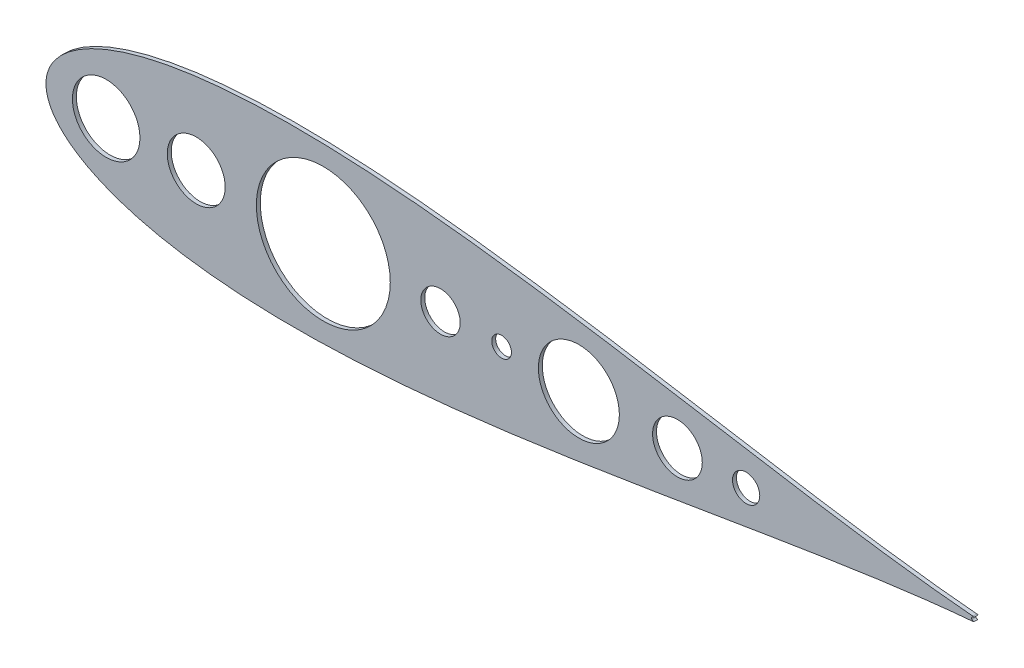
SolidWorks part; units mm, degrees
ref_plane "Front Plane" through (0, 0, 0) normal (0, 0, 1) x (1, 0, 0)
ref_plane "Top Plane" through (0, 0, 0) normal (0, 1, 0) x (1, 0, 0)
ref_plane "Right Plane" through (0, 0, 0) normal (1, 0, 0) x (0, 0, -1)
sketch "Model" plane through (0, 0, 0) normal (0, 0, 1) x (1, 0, 0)
  line L0 (786.347, 515.344) -> (786.347, 515.865)
  line L1 (784.9141, 514.1717) -> (785.37, 514.1717)
  line L2 (785.5654, 516.7117) -> (785.1095, 516.7117)
  line L3 (784.0675, 516.0604) -> (783.1903, 516.0604)
  line L4 (784.0675, 516.386) -> (784.0675, 516.0604)
  line L5 (783.2391, 516.386) -> (784.0675, 516.386)
  line L6 (783.4834, 518.0142) -> (783.2391, 516.386)
  line L7 (783.0906, 518.0142) -> (783.4834, 518.0142)
  line L8 (782.8463, 516.386) -> (783.0906, 518.0142)
  line L9 (782.0505, 518.0142) -> (781.8063, 516.386)
  line L10 (781.6577, 518.0142) -> (782.0505, 518.0142)
  line L11 (781.4135, 516.386) -> (781.6577, 518.0142)
  line L12 (780.4203, 516.386) -> (781.4135, 516.386)
  line L13 (780.4203, 516.0604) -> (780.4203, 516.386)
  line L14 (781.3647, 516.0604) -> (780.4203, 516.0604)
  line L15 (781.1886, 514.8881) -> (781.3647, 516.0604)
  line L16 (780.29, 514.8881) -> (781.1886, 514.8881)
  line L17 (780.29, 514.5625) -> (780.29, 514.8881)
  line L18 (781.1398, 514.5625) -> (780.29, 514.5625)
  line L19 (780.8762, 512.804) -> (781.1398, 514.5625)
  line L20 (781.27, 512.804) -> (780.8762, 512.804)
  line L21 (781.5336, 514.5625) -> (781.27, 512.804)
  line L22 (782.5726, 514.5625) -> (781.5336, 514.5625)
  line L23 (782.309, 512.804) -> (782.5726, 514.5625)
  line L24 (782.7028, 512.804) -> (782.309, 512.804)
  line L25 (782.9664, 514.5625) -> (782.7028, 512.804)
  line L26 (783.9372, 514.5625) -> (782.9664, 514.5625)
  line L27 (783.9372, 514.8881) -> (783.9372, 514.5625)
  line L28 (783.0153, 514.8881) -> (783.9372, 514.8881)
  line L29 (783.1903, 516.0604) -> (783.0153, 514.8881)
  line L30 (781.8063, 516.386) -> (782.8463, 516.386)
  line L31 (781.5824, 514.8881) -> (782.6214, 514.8881)
  line L32 (782.7975, 516.0604) -> (781.7575, 516.0604)
  line L33 (782.6214, 514.8881) -> (782.7975, 516.0604)
  line L34 (781.7575, 516.0604) -> (781.5824, 514.8881)
  circle A0 centre (390.1313, 511.9487) radius 18.669
  circle A1 centre (547.6113, 511.9487) radius 12.7
  circle A2 centre (586.9813, 511.9487) radius 6.35
  circle A3 centre (700.3234, 511.9487) radius 16.0288
  circle A4 centre (744.6175, 511.9487) radius 8.7799
  circle A5 centre (332.0731, 511.9487) radius 21.7634
  arc A6 (890.8162, 510.4774) -> (891.5484, 510.7448) centre (890.6938, 511.9487) ccw
  arc A7 (891.5489, 513.1522) -> (890.8162, 513.42) centre (890.6938, 511.9487) ccw
  arc A8 (891.5489, 513.1522) -> (891.5484, 510.7448) centre (891.2322, 511.9485) ccw
  circle A9 centre (636.7879, 511.9487) radius 26.1032
  circle A10 centre (472.0506, 511.9487) radius 43.167
  spline S0 degree 3 poles (890.8162, 513.42) (890.3349, 513.46) (886.7082, 513.7655) (879.5659, 514.4256) (868.9642, 515.5285) (857.2098, 516.8818) (844.3469, 518.4937) (830.4355, 520.3658) (815.5358, 522.4939) (799.7123, 524.867) (783.0322, 527.4682) (765.5654, 530.2744) (747.384, 533.2565) (728.5623, 536.3802) (709.1765, 539.6059) (689.3045, 542.8901) (669.0255, 546.185) (648.4208, 549.44) (627.5727, 552.6022) (606.5651, 555.6172) (585.4835, 558.4299) (564.4149, 560.9854) (543.4476, 563.23) (522.6717, 565.1117) (502.1785, 566.5817) (482.061, 567.5944) (462.4138, 568.109) (443.3327, 568.0899) (424.9152, 567.5068) (407.2601, 566.3367) (390.4682, 564.5628) (374.6421, 562.177) (359.8874, 559.1785) (346.3131, 555.5773) (334.0341, 551.3946) (323.1728, 546.6676) (313.8611, 541.4589) (306.2382, 535.8742) (300.4324, 530.0959) (296.5018, 524.4296) (294.31, 519.3174) (293.4249, 515.2165) (293.2233, 511.9487) (293.4249, 508.6808) (294.31, 504.5799) (296.5018, 499.4677) (300.4324, 493.8014) (306.2382, 488.0231) (313.8611, 482.4384) (323.1728, 477.2297) (334.0341, 472.5027) (346.3131, 468.32) (359.8874, 464.7188) (374.6421, 461.7204) (390.4682, 459.3346) (407.2601, 457.5606) (424.9152, 456.3906) (443.3327, 455.8074) (462.4138, 455.7883) (482.061, 456.3029) (502.1785, 457.3157) (522.6717, 458.7856) (543.4476, 460.6673) (564.4149, 462.9119) (585.4835, 465.4674) (606.5651, 468.2801) (627.5727, 471.2951) (648.4208, 474.4573) (669.0255, 477.7124) (689.3045, 481.0073) (709.1765, 484.2914) (728.5623, 487.5172) (747.384, 490.6408) (765.5654, 493.6229) (783.0322, 496.4291) (799.7123, 499.0303) (815.5358, 501.4035) (830.4355, 503.5316) (844.3469, 505.4037) (857.2098, 507.0155) (868.9642, 508.3689) (879.5659, 509.4717) (886.7082, 510.1319) (890.3349, 510.4373) (890.8162, 510.4774) knots 0.020157 0.020157 0.020157 0.020157 0.021271 0.028553 0.036781 0.04592 0.055932 0.066773 0.078397 0.090755 0.103793 0.117456 0.131686 0.146422 0.1616 0.177156 0.193024 0.209135 0.225421 0.241812 0.258238 0.274629 0.290914 0.307025 0.322893 0.338448 0.353626 0.368361 0.38259 0.396253 0.40929 0.421647 0.43327 0.444109 0.454119 0.463255 0.471479 0.478755 0.485052 0.490344 0.49461 0.497833 0.5 0.502167 0.50539 0.509656 0.514948 0.521245 0.528521 0.536745 0.545881 0.555891 0.56673 0.578353 0.59071 0.603747 0.61741 0.631639 0.646374 0.661552 0.677107 0.692975 0.709086 0.725371 0.741762 0.758188 0.774579 0.790865 0.806976 0.822844 0.8384 0.853578 0.868314 0.882544 0.896207 0.909245 0.921603 0.933227 0.944068 0.95408 0.963219 0.971447 0.978729 0.979843 0.979843 0.979843 0.979843
  spline S1 degree 3 poles (786.6085, 512.6737) (786.5542, 512.675) (786.4473, 512.6775) (786.2902, 512.6944) (786.1402, 512.7254) (785.9972, 512.767) (785.861, 512.8199) (785.732, 512.8856) (785.6095, 512.963) (785.4945, 513.0529) (785.3872, 513.1535) (785.2903, 513.2665) (785.2023, 513.3898) (785.1254, 513.525) (785.0563, 513.6702) (784.9994, 513.8273) (784.9494, 513.9949) (784.9261, 514.1118) (784.9141, 514.1717) knots 0 0 0 0 0.065541 0.128963 0.190377 0.250092 0.308548 0.366398 0.424542 0.48317 0.542243 0.601739 0.662506 0.724856 0.789128 0.856346 0.926295 1 1 1 1
  spline S2 degree 3 poles (786.6166, 513.1948) (786.6642, 513.1957) (786.7571, 513.1974) (786.8928, 513.2135) (787.0218, 513.2369) (787.1428, 513.273) (787.2574, 513.3177) (787.3639, 513.3738) (787.4638, 513.4396) (787.5557, 513.5144) (787.6383, 513.5963) (787.7111, 513.682) (787.773, 513.771) (787.8229, 513.864) (787.8623, 513.9604) (787.8891, 514.0607) (787.9078, 514.1639) (787.9093, 514.234) (787.91, 514.2694) knots 0 0 0 0 0.076072 0.148752 0.218403 0.28576 0.350598 0.414964 0.478069 0.541761 0.60435 0.664075 0.721464 0.777587 0.832644 0.887844 0.94346 1 1 1 1
  spline S3 degree 3 poles (785.7679, 513.4695) (785.7964, 513.4476) (785.8532, 513.4038) (785.9457, 513.3479) (786.0431, 513.2995) (786.1473, 513.2625) (786.2562, 513.2312) (786.3715, 513.2107) (786.4921, 513.1966) (786.5745, 513.1954) (786.6166, 513.1948) knots 0 0 0 0 0.118271 0.236178 0.355663 0.475904 0.600127 0.728608 0.861313 1 1 1 1
  spline S4 degree 3 poles (786.347, 515.865) (786.4098, 515.8661) (786.5329, 515.8682) (786.7127, 515.8934) (786.8847, 515.9284) (787.045, 515.9819) (787.1911, 516.0441) (787.3178, 516.1165) (787.4234, 516.1969) (787.5074, 516.2866) (787.5706, 516.3829) (787.6168, 516.4832) (787.6441, 516.5885) (787.6477, 516.6603) (787.6495, 516.6964) knots 0 0 0 0 0.110166 0.215787 0.318027 0.417574 0.51165 0.596162 0.672935 0.74367 0.810677 0.874059 0.936696 1 1 1 1
  spline S5 degree 3 poles (787.5122, 515.6493) (787.5662, 515.6232) (787.6733, 515.5715) (787.8192, 515.4701) (787.9517, 515.353) (788.0256, 515.2617) (788.0627, 515.2158) knots 0 0 0 0 0.25388 0.503009 0.750291 1 1 1 1
  spline S6 degree 3 poles (788.3659, 514.3131) (788.3633, 514.242) (788.3581, 514.1001) (788.3117, 513.8904) (788.2397, 513.6854) (788.1374, 513.4893) (788.0128, 513.3059) (787.8645, 513.1418) (787.6943, 513.0007) (787.5044, 512.8828) (787.2987, 512.7886) (787.0787, 512.7232) (786.8476, 512.6806) (786.6891, 512.6761) (786.6085, 512.6737) knots 0 0 0 0 0.079648 0.158922 0.239619 0.322609 0.406035 0.487602 0.569685 0.653036 0.737436 0.822478 0.909748 1 1 1 1
  spline S7 degree 3 poles (787.91, 514.2694) (787.9078, 514.3167) (787.9034, 514.4111) (787.8696, 514.5501) (787.8139, 514.6839) (787.736, 514.8104) (787.6412, 514.9277) (787.5303, 515.0323) (787.4026, 515.1186) (787.285, 515.1782) (787.1808, 515.2189) (787.0917, 515.246) (786.9919, 515.269) (786.8826, 515.2903) (786.7631, 515.3085) (786.6335, 515.3237) (786.4936, 515.3358) (786.3968, 515.3412) (786.347, 515.344) knots 0 0 0 0 0.066909 0.133485 0.201035 0.271234 0.34288 0.413836 0.485977 0.56023 0.599884 0.644055 0.691892 0.744688 0.801492 0.862858 0.929328 1 1 1 1
  spline S8 degree 3 poles (787.6495, 516.6964) (787.6489, 516.7229) (787.6477, 516.7757) (787.6326, 516.8528) (787.61, 516.9276) (787.5788, 516.9997) (787.5371, 517.0686) (787.4871, 517.1349) (787.4277, 517.1982) (787.3595, 517.2573) (787.2864, 517.3135) (787.2062, 517.3613) (787.1214, 517.4022) (787.0319, 517.4358) (786.9374, 517.4612) (786.8384, 517.4794) (786.7346, 517.4908) (786.6638, 517.4924) (786.6278, 517.4932) knots 0 0 0 0 0.055275 0.109966 0.163247 0.218076 0.273301 0.330909 0.390995 0.454176 0.518862 0.583311 0.648517 0.715031 0.782502 0.852323 0.924928 1 1 1 1
  spline S9 degree 3 poles (785.1095, 516.7117) (785.1219, 516.7628) (785.146, 516.8628) (785.1964, 517.0056) (785.2513, 517.1408) (785.3171, 517.2657) (785.389, 517.383) (785.4713, 517.4899) (785.5603, 517.5892) (785.6588, 517.6774) (785.762, 517.7572) (785.8715, 517.8252) (785.985, 517.8837) (786.1034, 517.9319) (786.2269, 517.9683) (786.3546, 517.9946) (786.4866, 518.0117) (786.5762, 518.0134) (786.6217, 518.0142) knots 0 0 0 0 0.072625 0.141977 0.208985 0.273957 0.336889 0.398745 0.460116 0.520825 0.580994 0.640152 0.698622 0.757271 0.816427 0.876254 0.937165 1 1 1 1
  spline S10 degree 3 poles (788.1054, 516.6944) (788.1037, 516.6407) (788.1004, 516.5356) (788.0724, 516.3821) (788.0251, 516.2375) (787.9597, 516.1011) (787.8751, 515.9738) (787.7725, 515.8552) (787.6513, 515.745) (787.5594, 515.6818) (787.5122, 515.6493) knots 0 0 0 0 0.128068 0.250608 0.37063 0.490072 0.610375 0.734313 0.863217 1 1 1 1
  spline S11 degree 3 poles (785.37, 514.1717) (785.3819, 514.1326) (785.405, 514.0565) (785.4443, 513.947) (785.4892, 513.8466) (785.5372, 513.7546) (785.5877, 513.6701) (785.6442, 513.5953) (785.7025, 513.5269) (785.7464, 513.4884) (785.7679, 513.4695) knots 0 0 0 0 0.14977 0.291316 0.425966 0.55216 0.671527 0.786122 0.895325 1 1 1 1
  spline S12 degree 3 poles (786.6278, 517.4932) (786.57, 517.4912) (786.457, 517.4873) (786.2941, 517.4527) (786.1427, 517.3976) (786.027, 517.3318) (785.9415, 517.2668) (785.8805, 517.2101) (785.8205, 517.1471) (785.7656, 517.0738) (785.71, 516.9954) (785.6594, 516.9077) (785.6103, 516.813) (785.5807, 516.7461) (785.5654, 516.7117) knots 0 0 0 0 0.122712 0.239685 0.351816 0.463766 0.520818 0.579448 0.640604 0.705298 0.773634 0.844669 0.920057 1 1 1 1
  spline S13 degree 3 poles (786.6217, 518.0142) (786.688, 518.0122) (786.8192, 518.0083) (787.0119, 517.9721) (787.1977, 517.9149) (787.3746, 517.8358) (787.539, 517.7383) (787.6852, 517.6223) (787.8113, 517.4899) (787.9171, 517.3437) (787.9999, 517.1874) (788.061, 517.0266) (788.0982, 516.8616) (788.103, 516.7502) (788.1054, 516.6944) knots 0 0 0 0 0.090254 0.17854 0.266093 0.354631 0.441886 0.525747 0.608114 0.690197 0.770821 0.848326 0.924012 1 1 1 1
  spline S14 degree 3 poles (788.0627, 515.2158) (788.0871, 515.1823) (788.1356, 515.1159) (788.1955, 515.0092) (788.2498, 514.9013) (788.2921, 514.7893) (788.3248, 514.6745) (788.3483, 514.5568) (788.3628, 514.436) (788.3649, 514.3542) (788.3659, 514.3131) knots 0 0 0 0 0.128136 0.254173 0.378112 0.501712 0.623986 0.747096 0.872875 1 1 1 1
sketch "Sketch2" plane through (0, 0, 0) normal (0, 0, 1) x (1, 0, 0)
  circle A0 centre (390.1313, 511.9487) radius 18.669
  circle A1 centre (547.6113, 511.9487) radius 12.7
  circle A2 centre (586.9813, 511.9487) radius 6.35
  circle A3 centre (700.3234, 511.9487) radius 16.0288
  circle A4 centre (744.6175, 511.9487) radius 8.7799
  circle A5 centre (332.0731, 511.9487) radius 21.7634
  arc A6 (890.8162, 510.4774) -> (891.5484, 510.7448) centre (890.6938, 511.9487) ccw
  arc A7 (891.5489, 513.1522) -> (890.8162, 513.42) centre (890.6938, 511.9487) ccw
  arc A8 (891.5489, 513.1522) -> (891.5484, 510.7448) centre (891.2322, 511.9485) ccw
  circle A9 centre (636.7879, 511.9487) radius 26.1032
  circle A10 centre (472.0506, 511.9487) radius 43.167
  spline S0 degree 3 poles (890.8162, 513.42) (890.3349, 513.46) (886.7082, 513.7655) (879.5659, 514.4256) (868.9642, 515.5285) (857.2098, 516.8818) (844.3469, 518.4937) (830.4355, 520.3658) (815.5358, 522.4939) (799.7123, 524.867) (783.0322, 527.4682) (765.5654, 530.2744) (747.384, 533.2565) (728.5623, 536.3802) (709.1765, 539.6059) (689.3045, 542.8901) (669.0255, 546.185) (648.4208, 549.44) (627.5727, 552.6022) (606.5651, 555.6172) (585.4835, 558.4299) (564.4149, 560.9854) (543.4476, 563.23) (522.6717, 565.1117) (502.1785, 566.5817) (482.061, 567.5944) (462.4138, 568.109) (443.3327, 568.0899) (424.9152, 567.5068) (407.2601, 566.3367) (390.4682, 564.5628) (374.6421, 562.177) (359.8874, 559.1785) (346.3131, 555.5773) (334.0341, 551.3946) (323.1728, 546.6676) (313.8611, 541.4589) (306.2382, 535.8742) (300.4324, 530.0959) (296.5018, 524.4296) (294.31, 519.3174) (293.4249, 515.2165) (293.2233, 511.9487) (293.4249, 508.6808) (294.31, 504.5799) (296.5018, 499.4677) (300.4324, 493.8014) (306.2382, 488.0231) (313.8611, 482.4384) (323.1728, 477.2297) (334.0341, 472.5027) (346.3131, 468.32) (359.8874, 464.7188) (374.6421, 461.7204) (390.4682, 459.3346) (407.2601, 457.5606) (424.9152, 456.3906) (443.3327, 455.8074) (462.4138, 455.7883) (482.061, 456.3029) (502.1785, 457.3157) (522.6717, 458.7856) (543.4476, 460.6673) (564.4149, 462.9119) (585.4835, 465.4674) (606.5651, 468.2801) (627.5727, 471.2951) (648.4208, 474.4573) (669.0255, 477.7124) (689.3045, 481.0073) (709.1765, 484.2914) (728.5623, 487.5172) (747.384, 490.6408) (765.5654, 493.6229) (783.0322, 496.4291) (799.7123, 499.0303) (815.5358, 501.4035) (830.4355, 503.5316) (844.3469, 505.4037) (857.2098, 507.0155) (868.9642, 508.3689) (879.5659, 509.4717) (886.7082, 510.1319) (890.3349, 510.4373) (890.8162, 510.4774) knots 0.020157 0.020157 0.020157 0.020157 0.021271 0.028553 0.036781 0.04592 0.055932 0.066773 0.078397 0.090755 0.103793 0.117456 0.131686 0.146422 0.1616 0.177156 0.193024 0.209135 0.225421 0.241812 0.258238 0.274629 0.290914 0.307025 0.322893 0.338448 0.353626 0.368361 0.38259 0.396253 0.40929 0.421647 0.43327 0.444109 0.454119 0.463255 0.471479 0.478755 0.485052 0.490344 0.49461 0.497833 0.5 0.502167 0.50539 0.509656 0.514948 0.521245 0.528521 0.536745 0.545881 0.555891 0.56673 0.578353 0.59071 0.603747 0.61741 0.631639 0.646374 0.661552 0.677107 0.692975 0.709086 0.725371 0.741762 0.758188 0.774579 0.790865 0.806976 0.822844 0.8384 0.853578 0.868314 0.882544 0.896207 0.909245 0.921603 0.933227 0.944068 0.95408 0.963219 0.971447 0.978729 0.979843 0.979843 0.979843 0.979843
extrude "Boss-Extrude1" add sketch "Sketch2" along normal blind 2.54
